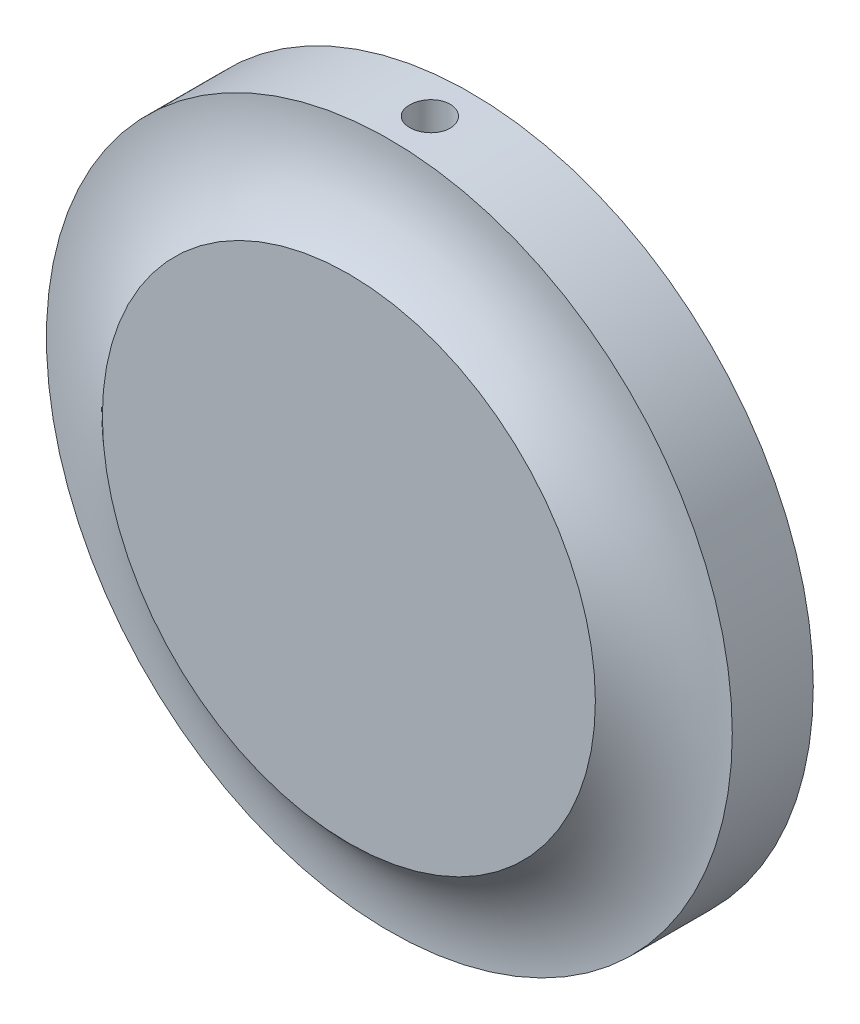
SolidWorks part; units mm, degrees
ref_plane "Front Plane" through (0, 0, 0) normal (0, 0, 1) x (1, 0, 0)
ref_plane "Top Plane" through (0, 0, 0) normal (0, 1, 0) x (1, 0, 0)
ref_plane "Right Plane" through (0, 0, 0) normal (1, 0, 0) x (0, 0, -1)
sketch "Sketch1" plane through (0, 0, 0) normal (0, 0, 1) x (1, 0, 0)
  circle A0 centre (0, 0) radius 25.4
  dimension "D1" = 50.8
extrude "Boss-Extrude1" add sketch "Sketch1" along normal blind 6 contours A0
sketch "Sketch2" plane through (0, 0, 0) normal (1, 0, 0) x (0, 0, -1)
  circle A0 centre (-13, 25.4) radius 10
  dimension "D1" = 20
  dimension "D2" = 3
revolve "Cut-Revolve1" cut sketch "Sketch2" angle 360 about axis through (0, 0, 6) along (0, 0, -1)
mirror "Mirror1" about plane through (0, 0, 0) normal (0, 0, 1) of bodies 102
ref_plane "Plane1" through (0, 15, 0) normal (0, 1, 0) x (1, 0, 0)
sketch "Sketch3" plane through (0, 15, 0) normal (0, 1, 0) x (1, 0, 0)
  circle A0 centre (0, 0) radius 1.5
  dimension "D1" = 3
extrude "Cut-Extrude1" cut sketch "Sketch3" along normal through all
